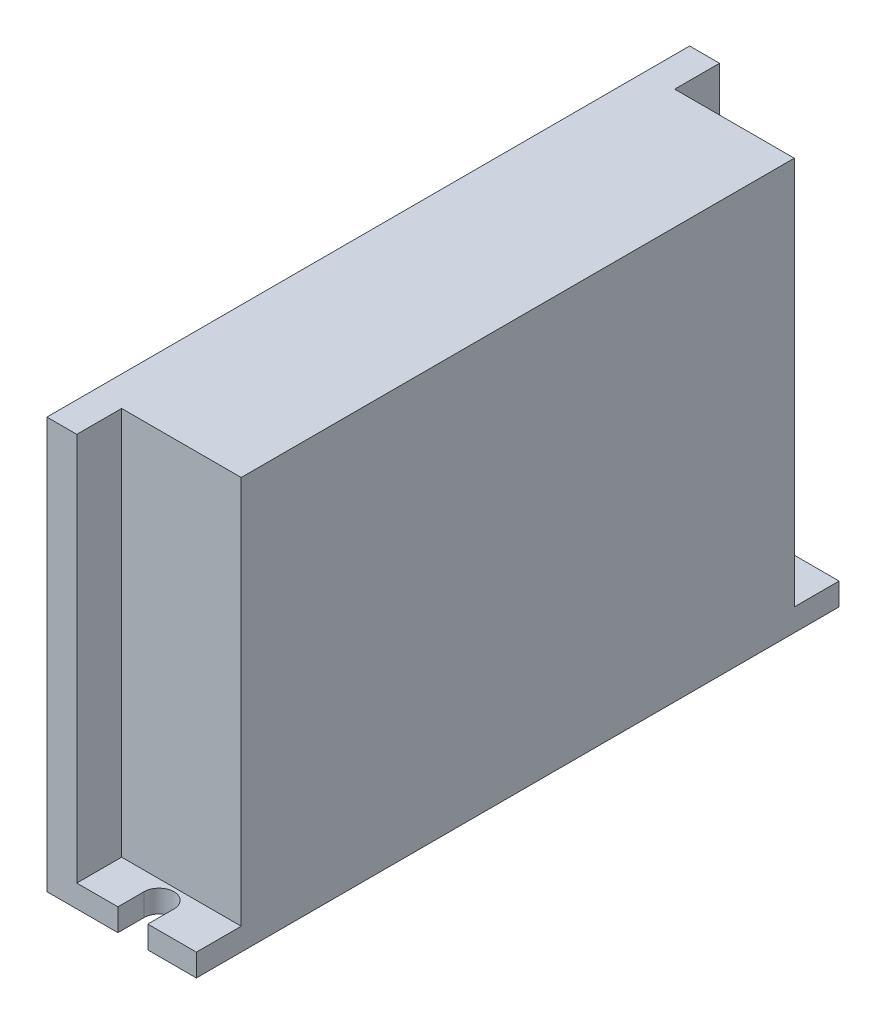
SolidWorks part; units mm, degrees
ref_plane "Front Plane" through (0, 0, 0) normal (0, 0, 1) x (1, 0, 0)
ref_plane "Top Plane" through (0, 0, 0) normal (0, 1, 0) x (1, 0, 0)
ref_plane "Right Plane" through (0, 0, 0) normal (1, 0, 0) x (0, 0, -1)
sketch "Sketch1" plane through (0, 0, 0) normal (0, 1, 0) x (1, 0, 0)
  line L1 (-10, -43) -> (10, -43)
  line L2 (-10, -43) -> (-10, 43)
  line L3 (-10, 43) -> (10, 43)
  line L4 (10, -43) -> (10, 43)
  line L5 (-10, -43) -> (10, 43) construction
  line L6 (-10, 43) -> (10, -43) construction
  point P0 (0, 0)
  dimension "D1" = 20
  dimension "D2" = 86
extrude "Boss-Extrude1" add sketch "Sketch1" along normal blind 3
sketch "Sketch2" plane through (0, 3, 0) normal (0, 1, 0) x (1, 0, 0)
  line L0 (10, 0) -> (-10, 0) construction
  line L1 (10, -43) -> (10, 43) construction
  line L2 (-10, 43) -> (-10, -43) construction
  line L3 (-0.5, 39.5) -> (-0.5, 43)
  line L4 (10, 43) -> (-10, 43) construction
  line L5 (3.5, 39.5) -> (3.5, 43)
  line L6 (-0.5, -39.5) -> (-0.5, -43)
  line L7 (-10, -43) -> (10, -43) construction
  line L8 (3.5, -39.5) -> (3.5, -43)
  line L9 (3.5, 43) -> (-0.5, 43)
  line L10 (3.5, -43) -> (-0.5, -43)
  arc A0 (-0.5, 39.5) -> (3.5, 39.5) centre (1.5, 39.5) ccw
  arc A1 (3.5, -39.5) -> (-0.5, -39.5) centre (1.5, -39.5) ccw
  dimension "D1" = 4
  dimension "D2" = 79
  dimension "D3" = 11.5
extrude "Cut-Extrude1" cut sketch "Sketch2" against normal through all
sketch "Sketch3" plane through (0, 3, 0) normal (0, 1, 0) x (1, 0, 0)
  line L0 (-10, -43) -> (-0.5, -43) construction
  line L1 (-10, 43) -> (-6, 43)
  line L2 (-10, 43) -> (-10, -43)
  line L3 (-10, -43) -> (-6, -43)
  line L4 (-6, 43) -> (-6, -43)
  dimension "D1" = 4
extrude "Boss-Extrude2" add sketch "Sketch3" along normal blind 52
sketch "Sketch4" plane through (0, 3, 0) normal (0, 1, 0) x (1, 0, 0)
  line L0 (10, -43) -> (10, 43) construction
  line L1 (10, 37) -> (-6, 37)
  line L2 (10, 37) -> (10, -37)
  line L3 (10, -37) -> (-6, -37)
  line L4 (-6, 37) -> (-6, -37)
  line L5 (-6, -43) -> (-6, 43) construction
  line L6 (10, 0) -> (-6, 0) construction
  line L7 (10, 43) -> (3.5, 43) construction
  dimension "D1" = 6
extrude "Boss-Extrude3" add sketch "Sketch4" along normal blind 52
sketch "Sketch5" plane through (0, 55, 0) normal (0, 1, 0) x (1, 0, 0)
  line L1 (-5.8052, 33.9424) -> (5.4497, 33.9424)
  line L2 (-5.8052, 33.9424) -> (-5.8052, 17.9486)
  line L3 (-5.8052, 17.9486) -> (5.4497, 17.9486)
  line L4 (5.4497, 33.9424) -> (5.4497, 17.9486)
